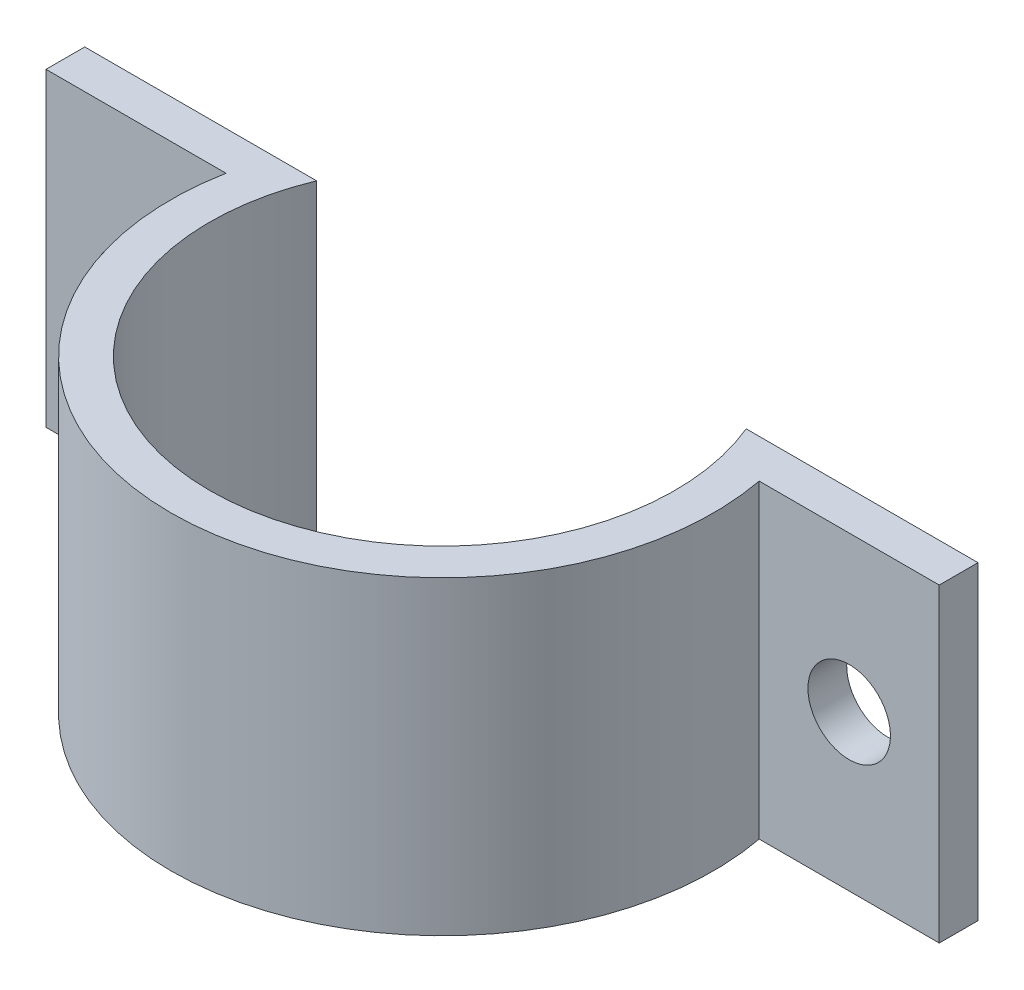
SolidWorks part; units mm, degrees
ref_plane "Front Plane" through (0, 0, 0) normal (0, 0, 1) x (1, 0, 0)
ref_plane "Top Plane" through (0, 0, 0) normal (0, 1, 0) x (1, 0, 0)
ref_plane "Right Plane" through (0, 0, 0) normal (1, 0, 0) x (0, 0, -1)
sketch "Sketch1" plane through (0, 0, 0) normal (0, 1, 0) x (1, 0, 0)
  line L0 (0, 0) -> (32.2155, 0) construction
  line L1 (0, 8.89) -> (38.1, 8.89) construction
  line L2 (0, 0) -> (0, 41.8211) construction
  line L3 (-36.5874, 13.6525) -> (36.5874, 13.6525) construction
  line L4 (-36.5874, 4.1275) -> (36.5874, 4.1275) construction
  line L5 (36.5874, 13.6525) -> (17.5374, 13.6525)
  line L6 (36.5874, 13.6525) -> (36.5874, 4.1275)
  line L7 (36.5874, 4.1275) -> (21.8384, 4.1275)
  line L8 (-17.5374, 13.6525) -> (-36.5874, 13.6525)
  line L9 (-36.5874, 13.6525) -> (-36.5874, 4.1275)
  line L10 (-36.5874, 4.1275) -> (-21.8384, 4.1275)
  circle A0 centre (0, 0) radius 19.05
  circle A1 centre (0, 0) radius 22.225 construction
  arc A3 (-21.8384, 4.1275) -> (21.8384, 4.1275) centre (0, 0) ccw
  arc A5 (17.5374, 13.6525) -> (-17.5374, 13.6525) centre (0, 0) ccw
  point P13 (0, 13.6525)
  point P14 (0, 4.1275)
  dimension "D1" = 38.1
  dimension "D2" = 44.45
  dimension "D3" = 8.89
  dimension "D4" = 38.1
  dimension "D5" = 4.7625
  dimension "D6" = 19.05
extrude "Boss-Extrude1" add sketch "Sketch1" along normal blind 25.4
sketch "Sketch2" plane through (0, 0, -13.6525) normal (0, 0, -1) x (-1, 0, 0)
  line L3 (36.5874, 12.7) -> (17.5374, 12.7) construction
  line L4 (36.5874, 25.4) -> (36.5874, 0) construction
  line L5 (17.5374, 25.4) -> (17.5374, 0) construction
  line L6 (0, 0) -> (0, 25.4) construction
  line L7 (-17.5374, 0) -> (17.5374, 0) construction
  line L8 (17.5374, 25.4) -> (-17.5374, 25.4) construction
  circle A0 centre (29.21, 12.7) radius 3.3782
  circle A1 centre (-29.21, 12.7) radius 3.3782
  dimension "D1" = 6.7564
  dimension "D2" = 29.21
extrude "Cut-Extrude1" cut sketch "Sketch2" against normal through all
sketch "Sketch3" plane through (0, 25.4, 0) normal (0, 1, 0) x (1, 0, 0)
  line L0 (-36.5874, 8.89) -> (42.4749, 8.89) construction
  line L1 (-36.5874, 13.6525) -> (-36.5874, 4.1275) construction
  line L2 (42.4749, 7.3025) -> (-41.652, 7.3025) construction
  line L4 (42.4749, 7.3025) -> (-41.652, 7.3025)
  line L5 (42.4749, 7.3025) -> (42.4749, 31.4433)
  line L6 (42.4749, 31.4433) -> (-41.652, 31.4433)
  line L7 (-41.652, 7.3025) -> (-41.652, 31.4433)
  dimension "D1" = 1.5875
extrude "Cut-Extrude2" cut sketch "Sketch3" against normal through all
